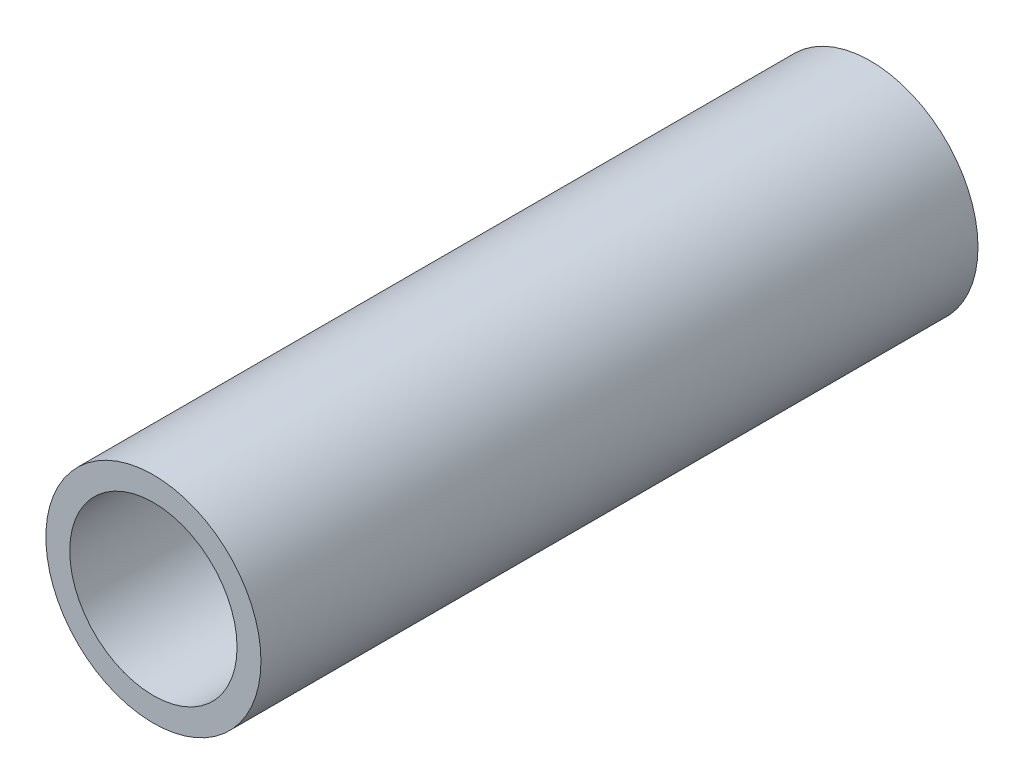
SolidWorks part; units mm, degrees
material "Plain Carbon Steel"
ref_plane "Front Plane" through (0, 0, 0) normal (0, 0, 1) x (1, 0, 0)
ref_plane "Top Plane" through (0, 0, 0) normal (0, 1, 0) x (1, 0, 0)
ref_plane "Right Plane" through (0, 0, 0) normal (1, 0, 0) x (0, 0, -1)
sketch "Sketch1" plane through (0, 0, 0) normal (0, 0, 1) x (1, 0, 0)
  circle A0 centre (0, 0) radius 2.25
  circle A1 centre (0, 0) radius 1.75
  dimension "D1" = 4.5
  dimension "D2" = 3.5
extrude "Boss-Extrude1" add sketch "Sketch1" along normal blind 15
